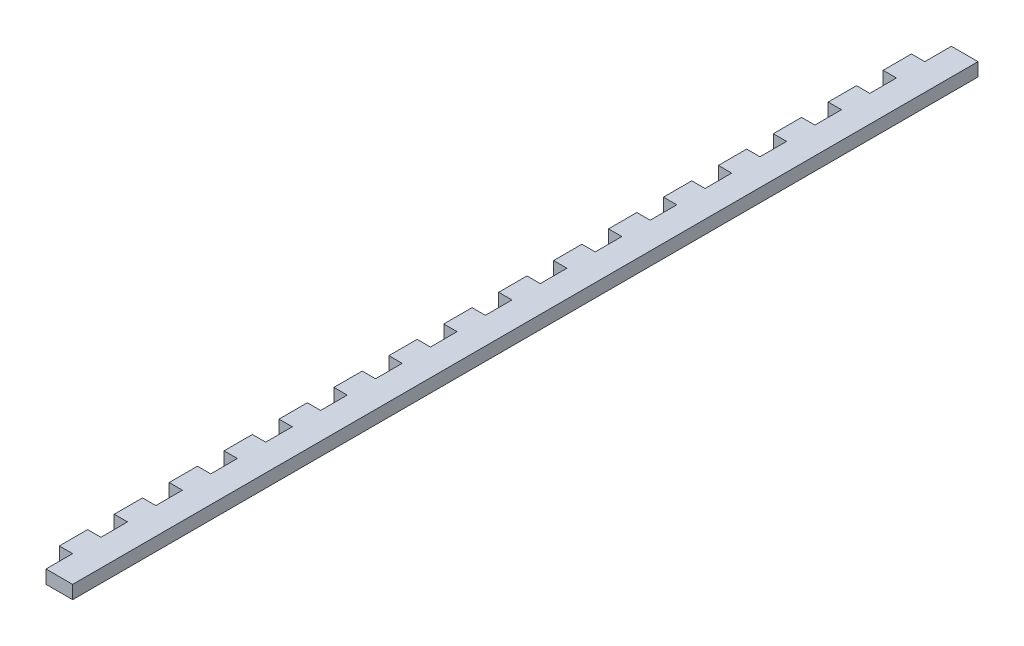
SolidWorks part; units mm, degrees
material "Acrylic (Medium-high impact)"
ref_plane "Front" through (0, 0, 0) normal (0, 0, 1) x (1, 0, 0)
ref_plane "Top" through (0, 0, 0) normal (0, 1, 0) x (1, 0, 0)
ref_plane "Right" through (0, 0, 0) normal (1, 0, 0) x (0, 0, -1)
sketch "Sketch1" plane through (0, 0, 0) normal (1, 0, 0) x (0, 0, -1)
  line L1 (-215.9, 142.875) -> (215.9, 142.875)
  line L2 (-215.9, 142.875) -> (-215.9, -142.875)
  line L3 (-215.9, -142.875) -> (215.9, -142.875)
  line L4 (215.9, 142.875) -> (215.9, -142.875)
  point P4 (-215.9, 0)
  point P6 (0, 142.875)
  dimension "D1" = 285.75
  dimension "D2" = 431.8
extrude "Boss-Extrude1" add sketch "Sketch1" along normal blind 6.35
sketch "Sketch2" plane through (6.35, 0, 0) normal (1, 0, 0) x (0, 0, -1)
  line L0 (215.9, -142.875) -> (215.9, 142.875) construction
  line L1 (-215.9, 142.875) -> (215.9, 142.875)
  line L2 (-215.9, 142.875) -> (-215.9, 136.525)
  line L3 (-215.9, 136.525) -> (215.9, 136.525)
  line L4 (215.9, 142.875) -> (215.9, 136.525)
  dimension "D1" = 6.35
extrude "Boss-Extrude2" add sketch "Sketch2" along normal blind 12.7
sketch "Sketch3" plane through (0, 0, 0) normal (-1, 0, 0) x (0, 0, 1)
  line L0 (-190.5, -85.725) -> (0, -85.725)
  line L1 (0, -111.125) -> (-190.5, -111.125)
  line L2 (38.1, 142.875) -> (38.1, -142.875) construction
  line L3 (-215.9, 142.875) -> (215.9, 142.875) construction
  line L4 (215.9, -142.875) -> (-215.9, -142.875) construction
  line L5 (215.9, 142.875) -> (215.9, -142.875) construction
  arc A0 (0, -85.725) -> (0, -111.125) centre (0, -98.425) cw
  arc A1 (-190.5, -111.125) -> (-190.5, -85.725) centre (-190.5, -98.425) cw
  dimension "D1" = 25.4
  dimension "D3" = 190.5
  dimension "D2" = 38.1
  dimension "D4" = 177.8
  dimension "D5" = 44.45
extrude "Cut-Extrude1" cut sketch "Sketch3" against normal through all
sketch "Sketch4" plane through (0, 0, 0) normal (-1, 0, 0) x (0, 0, 1)
  line L0 (-189.7062, 142.875) -> (-177.0062, 142.875)
  line L1 (-215.9, 142.875) -> (-203.2, 142.875)
  line L2 (-215.9, 142.875) -> (-215.9, 136.525)
  line L3 (-215.9, 136.525) -> (-203.2, 136.525)
  line L4 (-203.2, 142.875) -> (-203.2, 136.525)
  line L5 (-189.7062, 142.875) -> (-189.7062, 136.525)
  line L6 (-189.7062, 136.525) -> (-177.0062, 136.525)
  line L7 (-177.0062, 142.875) -> (-177.0062, 136.525)
  line L8 (-163.5125, 142.875) -> (-150.8125, 142.875)
  line L9 (-163.5125, 142.875) -> (-163.5125, 136.525)
  line L10 (-163.5125, 136.525) -> (-150.8125, 136.525)
  line L11 (-150.8125, 142.875) -> (-150.8125, 136.525)
  line L12 (-137.3187, 142.875) -> (-124.6187, 142.875)
  line L13 (-137.3187, 142.875) -> (-137.3187, 136.525)
  line L14 (-137.3187, 136.525) -> (-124.6187, 136.525)
  line L15 (-124.6187, 142.875) -> (-124.6187, 136.525)
  line L16 (-111.125, 142.875) -> (-98.425, 142.875)
  line L17 (-111.125, 142.875) -> (-111.125, 136.525)
  line L18 (-111.125, 136.525) -> (-98.425, 136.525)
  line L19 (-98.425, 142.875) -> (-98.425, 136.525)
  line L20 (-84.9312, 142.875) -> (-72.2312, 142.875)
  line L21 (-84.9312, 142.875) -> (-84.9312, 136.525)
  line L22 (-84.9312, 136.525) -> (-72.2312, 136.525)
  line L23 (-72.2312, 142.875) -> (-72.2312, 136.525)
  line L24 (-58.7375, 142.875) -> (-46.0375, 142.875)
  line L25 (-58.7375, 142.875) -> (-58.7375, 136.525)
  line L26 (-58.7375, 136.525) -> (-46.0375, 136.525)
  line L27 (-46.0375, 142.875) -> (-46.0375, 136.525)
  line L28 (-32.5437, 142.875) -> (-19.8437, 142.875)
  line L29 (-32.5437, 142.875) -> (-32.5437, 136.525)
  line L30 (-32.5437, 136.525) -> (-19.8437, 136.525)
  line L31 (-19.8437, 142.875) -> (-19.8437, 136.525)
  line L32 (-6.35, 142.875) -> (6.35, 142.875)
  line L33 (-6.35, 142.875) -> (-6.35, 136.525)
  line L34 (-6.35, 136.525) -> (6.35, 136.525)
  line L35 (6.35, 142.875) -> (6.35, 136.525)
  line L36 (19.8438, 142.875) -> (32.5438, 142.875)
  line L37 (19.8438, 142.875) -> (19.8438, 136.525)
  line L38 (19.8438, 136.525) -> (32.5438, 136.525)
  line L39 (32.5438, 142.875) -> (32.5438, 136.525)
  line L40 (46.0375, 142.875) -> (58.7375, 142.875)
  line L41 (46.0375, 142.875) -> (46.0375, 136.525)
  line L42 (46.0375, 136.525) -> (58.7375, 136.525)
  line L43 (58.7375, 142.875) -> (58.7375, 136.525)
  line L44 (72.2313, 142.875) -> (84.9313, 142.875)
  line L45 (72.2313, 142.875) -> (72.2313, 136.525)
  line L46 (72.2313, 136.525) -> (84.9313, 136.525)
  line L47 (84.9313, 142.875) -> (84.9313, 136.525)
  line L48 (98.425, 142.875) -> (111.125, 142.875)
  line L49 (98.425, 142.875) -> (98.425, 136.525)
  line L50 (98.425, 136.525) -> (111.125, 136.525)
  line L51 (111.125, 142.875) -> (111.125, 136.525)
  line L52 (124.6188, 142.875) -> (137.3187, 142.875)
  line L53 (124.6188, 142.875) -> (124.6188, 136.525)
  line L54 (124.6188, 136.525) -> (137.3187, 136.525)
  line L55 (137.3187, 142.875) -> (137.3187, 136.525)
  line L56 (150.8125, 142.875) -> (163.5125, 142.875)
  line L57 (150.8125, 142.875) -> (150.8125, 136.525)
  line L58 (150.8125, 136.525) -> (163.5125, 136.525)
  line L59 (163.5125, 142.875) -> (163.5125, 136.525)
  line L60 (177.0062, 142.875) -> (189.7062, 142.875)
  line L61 (177.0062, 142.875) -> (177.0062, 136.525)
  line L62 (177.0062, 136.525) -> (189.7062, 136.525)
  line L63 (189.7062, 142.875) -> (189.7062, 136.525)
  line L64 (203.2, 142.875) -> (215.9, 142.875)
  line L65 (203.2, 142.875) -> (203.2, 136.525)
  line L66 (203.2, 136.525) -> (215.9, 136.525)
  line L67 (215.9, 142.875) -> (215.9, 136.525)
  point P5 (0, 0)
  dimension "D1" = 6.35
  dimension "D2" = 12.7
  dimension "D3" = 17
sketch "Sketch5" plane through (0, 0, -215.9) normal (0, 0, -1) x (-1, 0, 0)
  line L1 (-6.35, 136.525) -> (27.1124, 136.525)
  line L2 (-6.35, 136.525) -> (-6.35, -158.2545)
  line L3 (-6.35, -158.2545) -> (27.1124, -158.2545)
  line L4 (27.1124, 136.525) -> (27.1124, -158.2545)
extrude "Cut-Extrude2" cut sketch "Sketch5" against normal through all
extrude "Cut-Extrude3" cut sketch "Sketch4" against normal blind 6.35
